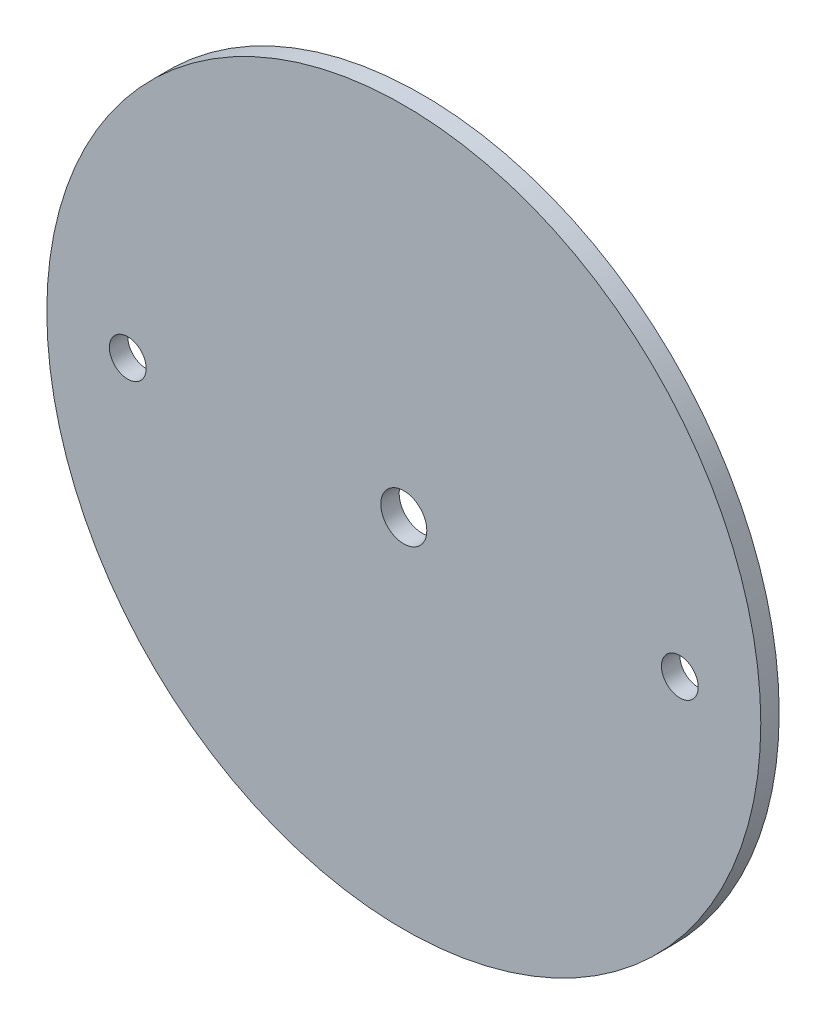
SolidWorks part; units mm, degrees
ref_plane "Front Plane" through (0, 0, 0) normal (0, 0, 1) x (1, 0, 0)
ref_plane "Top Plane" through (0, 0, 0) normal (0, 1, 0) x (1, 0, 0)
ref_plane "Right Plane" through (0, 0, 0) normal (1, 0, 0) x (0, 0, -1)
sketch "Sketch1" plane through (0, 0, 0) normal (0, 0, 1) x (1, 0, 0)
  circle A0 centre (0, 0) radius 61.595
  dimension "D1" = 123.19
extrude "Boss-Extrude1" add sketch "Sketch1" along normal mid plane 3.175
sketch "Sketch2" plane through (0, 0, 1.5875) normal (0, 0, 1) x (1, 0, 0)
  line L0 (-1000, 0) -> (49000, 0) construction
  line L1 (0, -1000) -> (0, 49000) construction
  point P4 (47.625, 0)
  point P5 (-47.625, 0)
  dimension "D2" = 95.25
  dimension "D1" = 47.625
hole_wizard "1/4 (0.25) Diameter Hole1" positions "Sketch2" profile "Sketch3" hole size "1/4" standard "ANSI Inch" end condition through all
sketch "Sketch3" plane through (-47.625, 0, 1.5875) normal (1, 0, 0) x (0, -1, 0)
  line L0 (0, 0) -> (0, 3.175)
  line L1 (0, 3.175) -> (3.175, 3.175)
  line L2 (3.175, 3.175) -> (3.175, 0)
  line L5 (3.175, 0) -> (0, 0)
  line L11 (0, -6.35) -> (0, 107.95) construction
  dimension "Thru Hole Dia." = 6.35
  dimension "Thru Hole Depth" = 3.175
sketch "Sketch4" plane through (0, 0, 1.5875) normal (0, 0, 1) x (1, 0, 0)
  point P0 (0, 0)
hole_wizard "5/16 (0.3125) Diameter Hole1" positions "Sketch4" profile "Sketch5" hole size "5/16" standard "ANSI Inch"
sketch "Sketch5" plane through (0, 0, 1.5875) normal (1, 0, 0) x (0, -1, 0)
  line L0 (0, 0) -> (0, 3.302)
  line L1 (0, 3.302) -> (3.9687, 3.302)
  line L2 (3.9687, 3.302) -> (3.9688, 0)
  line L5 (3.9688, 0) -> (0, 0)
  line L10 (0, 3.302) -> (-3.9688, 3.302) construction
  line L11 (0, -6.35) -> (0, 107.95) construction
  dimension "Hole Dia." = 7.9375
  dimension "Hole Depth" = 3.302
  dimension "Drill Angle" = 180
equation "\"AIRFRAME_OD\"= 5.15in"
equation "\"AIRFRAME_ID\"= 4.99in"
equation "\"FLAT_T\"= 0.125in"
equation "\"NOSE_EXP_L\"= 27in"
equation "\"NOSE_SHOULDER_L\"= 5in"
equation "\"MAIN_L\"= 30in"
equation "\"RECO_COUP_L\"= 10in"
equation "\"RECO_SWITCH_L\"= 2in"
equation "\"DROGUE_L\"= 20in"
equation "\"ATS_FORE_COUP_L\"= 5.5in"
equation "\"ATS_AFT_COUP_L\"= 4.5in"
equation "\"LOWER_L\"= 30in"
equation "\"FIN_N\"= 4"
equation "\"CR_AFT_X\"= 0.5in"
equation "\"CR_FORE_X\"= 9.25in"
equation "\"FIN_ROOT\"= 8in"
equation "\"FIN_X\"= 0.75in"
equation "\"MOTOR_OD\"= 3.091in"
equation "\"MOTOR_ID\"= 3.00in"
equation "\"COUPLER_OD\"= 4.998in"
equation "\"COUPLER_ID\"= 4.85in"
equation "\"D1@Sketch1\"=\"COUPLER_ID\""
equation "\"D1@Boss-Extrude1\"=\"FLAT_T\""
equation "\"RECO_ROD_X\"= 3.5in"
equation "\"ATS_ROD_X\"= 3.75in"
equation "\"D2@Sketch2\"=\"ATS_ROD_X\""
equation "\"MOTOR_L\"= 14in"
equation "\"MOTOR_LOWER_X\"= 2in"
equation "\"D1@Sketch2\"=\"ATS_ROD_X\"/2"
